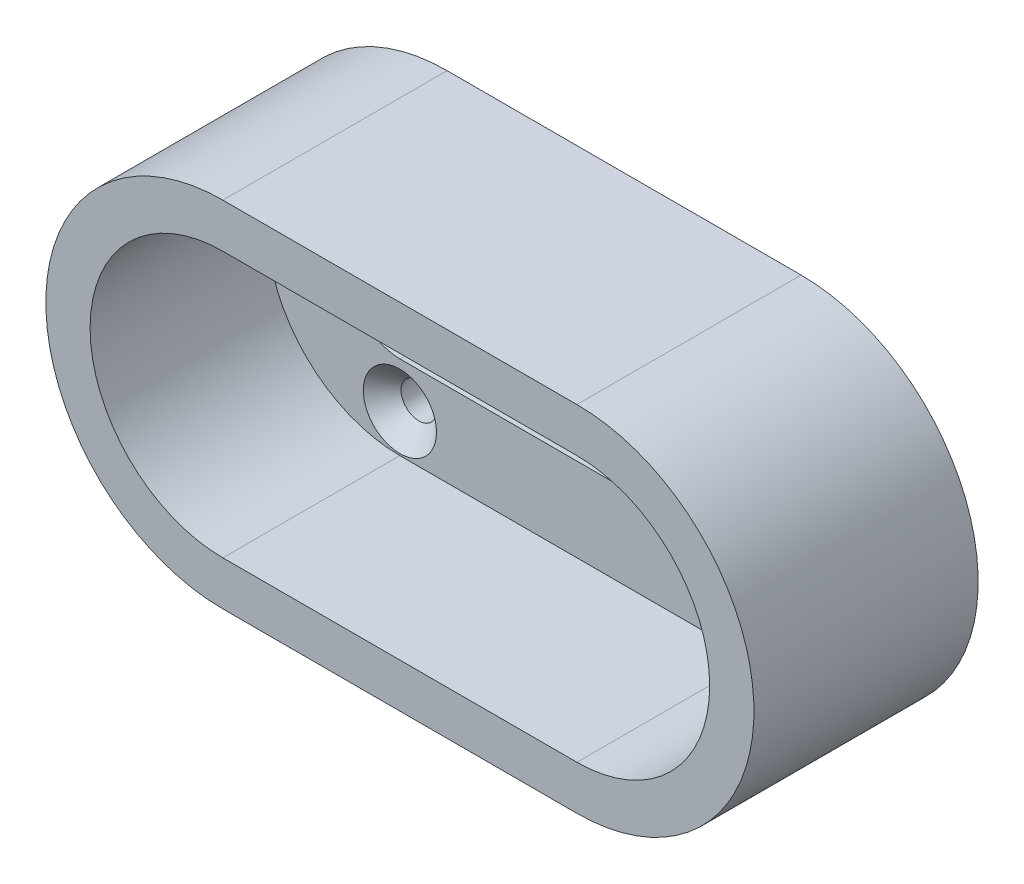
SolidWorks part; units mm, degrees
ref_plane "Front Plane" through (0, 0, 0) normal (0, 0, 1) x (1, 0, 0)
ref_plane "Top Plane" through (0, 0, 0) normal (0, 1, 0) x (1, 0, 0)
ref_plane "Right Plane" through (0, 0, 0) normal (1, 0, 0) x (0, 0, -1)
sketch "Sketch2" plane through (0, 0, 0) normal (0, 0, 1) x (1, 0, 0)
  line L0 (-15, 0) -> (15, 0) construction
  line L1 (-15, 15) -> (15, 15)
  line L2 (-15, -15) -> (15, -15)
  line L3 (-15, 8) -> (-15, 0) construction
  line L4 (-15, 0) -> (-15, -8) construction
  line L5 (-15, -8) -> (-23, 0) construction
  line L6 (-23, 0) -> (-15, 8) construction
  line L7 (0, 15) -> (0, -15) construction
  line L8 (23, 0) -> (15, 8) construction
  line L9 (15, -8) -> (23, 0) construction
  line L10 (15, 0) -> (15, -8) construction
  line L11 (15, 8) -> (15, 0) construction
  line L12 (-15, 0) -> (15, 0) construction
  line L13 (-15, 4.15) -> (15, 4.15)
  line L14 (-15, -4.15) -> (15, -4.15)
  arc A0 (-15, 15) -> (-15, -15) centre (-15, 0) ccw
  arc A1 (15, -15) -> (15, 15) centre (15, 0) ccw
  circle A2 centre (-15, 8) radius 1.5
  circle A3 centre (-23, 0) radius 1.5
  circle A4 centre (-15, -8) radius 1.5
  circle A5 centre (15, -8) radius 1.5
  circle A6 centre (23, 0) radius 1.5
  circle A7 centre (15, 8) radius 1.5
  arc A8 (-15, 4.15) -> (-15, -4.15) centre (-15, 0) ccw
  arc A9 (15, -4.15) -> (15, 4.15) centre (15, 0) ccw
  point P3 (0, 0)
  point P24 (0, 0)
  dimension "D1" = 3
  dimension "D2" = 8
  dimension "D3" = 8
  dimension "D4" = 15
  dimension "D6" = 4.15
  dimension "D5" = 30
extrude "Boss-Extrude1" add sketch "Sketch2" along normal blind 4
sketch "Sketch3" plane through (0, 0, 4) normal (0, 0, 1) x (1, 0, 0)
  line L0 (-15, 0) -> (15, 0) construction
  line L1 (-15, 11.25) -> (15, 11.25)
  line L2 (-15, -15) -> (15, -15)
  line L3 (15, 15) -> (-15, 15)
  line L4 (-15, -15) -> (15, -15)
  line L5 (15, 15) -> (-15, 15)
  line L6 (-15, -11.25) -> (15, -11.25)
  arc A0 (-15, 11.25) -> (-15, -11.25) centre (-15, 0) ccw
  arc A1 (15, -11.25) -> (15, 11.25) centre (15, 0) ccw
  arc A2 (-15, 15) -> (-15, -15) centre (-15, 0) ccw
  arc A3 (15, -15) -> (15, 15) centre (15, 0) ccw
  arc A4 (-15, 15) -> (-15, -15) centre (-15, 0) ccw
  arc A5 (15, -15) -> (15, 15) centre (15, 0) ccw
  point P0 (0, 0)
  point P11 (-15, 0)
  point P13 (-15, 14.6565)
  dimension "D2" = 11.25
  dimension "D1" = 0
extrude "Boss-Extrude2" add sketch "Sketch3" along normal blind 15
chamfer "Chamfer1" distance 1.6 angle 45 6 edges at (13.5, -8, 4) (21.5, 0, 4) (13.5, 8, 4) (-13.5, -8, 4) (-21.5, 0, 4) (-13.5, 8, 4)
